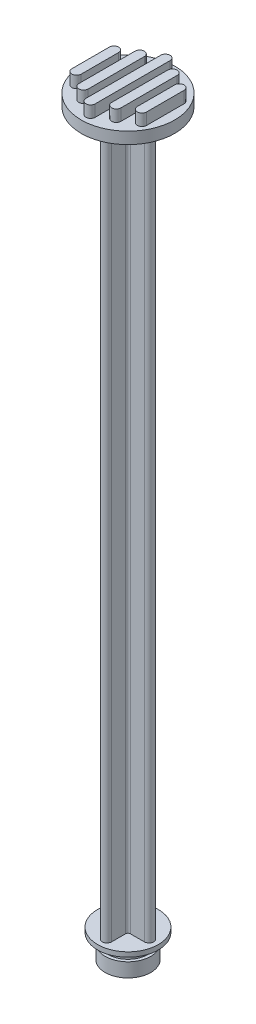
SolidWorks part; units mm, degrees
ref_plane "Front Plane" through (0, 0, 0) normal (0, 0, 1) x (1, 0, 0)
ref_plane "Top Plane" through (0, 0, 0) normal (0, 1, 0) x (1, 0, 0)
ref_plane "Right Plane" through (0, 0, 0) normal (1, 0, 0) x (0, 0, -1)
sketch "Sketch1" plane through (0, 0, 0) normal (0, 0, 1) x (1, 0, 0)
  line L0 (0, 0) -> (4.875, 0)
  line L1 (4.875, 0) -> (4.875, 3)
  line L2 (4.875, 3) -> (4.225, 3)
  line L3 (4.225, 3) -> (4.225, 5)
  line L4 (4.225, 5) -> (6.5, 5)
  line L5 (6.5, 5) -> (6.5, 6)
  line L6 (6.5, 6) -> (0, 6)
  line L7 (0, 6) -> (0, 0)
  dimension "D1" = 6.5
  dimension "D2" = 1
  dimension "D3" = 2
  dimension "D4" = 3
  dimension "D5" = 4.875
  dimension "D6" = 4.225
revolve "Revolve1" add sketch "Sketch1" angle 360 about L7
sketch "Sketch2" plane through (0, 6, 0) normal (0, 1, 0) x (1, 0, 0)
  line L0 (0, 1) -> (0, 0) construction
  line L1 (-1, 0) -> (0, 0) construction
  line L2 (-1, 4.5) -> (-1, 1.5)
  line L3 (-4.5, -1) -> (-1.5, -1)
  line L4 (1, 4.5) -> (1, 1.5)
  line L5 (-4.5, 1) -> (-1.5, 1)
  line L6 (-1, 6.5) -> (-1, -6.5) construction
  line L7 (0, 6.5) -> (0, -6.5) construction
  line L8 (1, 6.5) -> (1, -6.5) construction
  line L9 (-6.5, 1) -> (6.5, 1) construction
  line L10 (-6.5, 0) -> (6.5, 0) construction
  line L11 (-6.5, -1) -> (6.5, -1) construction
  line L12 (1.5, -1) -> (4.5, -1)
  line L13 (0, -1) -> (0, -5.5) construction
  line L14 (1, -1.5) -> (1, -4.5)
  line L15 (1.5, 1) -> (4.5, 1)
  line L16 (-1, -1.5) -> (-1, -4.5)
  arc A1 (1, 4.5) -> (-1, 4.5) centre (0, 4.5) ccw
  arc A2 (4.5, -1) -> (4.5, 1) centre (4.5, 0) ccw
  arc A3 (1, -4.5) -> (-1, -4.5) centre (0, -4.5) cw
  arc A4 (-4.5, -1) -> (-4.5, 1) centre (-4.5, 0) cw
  arc A5 (-1.5, 1) -> (-1, 1.5) centre (-1.5, 1.5) ccw
  arc A6 (1, 1.5) -> (1.5, 1) centre (1.5, 1.5) ccw
  arc A7 (1.5, -1) -> (1, -1.5) centre (1.5, -1.5) ccw
  arc A8 (-1, -1.5) -> (-1.5, -1) centre (-1.5, -1.5) ccw
  point P19 (0, 0)
  point P42 (1, -1)
  point P45 (-1, -1)
  dimension "D5" = 0.5
  dimension "D3" = 4.5
  dimension "D4" = 4.5
  dimension "D1" = 1
  dimension "D2" = 1
extrude "Boss-Extrude1" add sketch "Sketch2" along normal blind 152
sketch "Sketch3" plane through (0, 158, 0) normal (0, 1, 0) x (1, 0, 0)
  circle A0 centre (0, 0) radius 10
  dimension "D1" = 20
extrude "Boss-Extrude2" add sketch "Sketch3" along normal blind 2.5
sketch "Sketch4" plane through (0, 160.5, 0) normal (0, 1, 0) x (1, 0, 0)
  line L0 (0, 6.3392) -> (0, -10) construction
  line L1 (-10, 0) -> (10, 0) construction
  line L2 (-3.5, 4.0448) -> (-3.5, -6.1505) construction
  line L3 (-1, 10) -> (-1, -10) construction
  line L4 (-1, 8) -> (-1, -10)
  line L5 (-4.5, 6) -> (-4.5, -6.1505)
  line L6 (-8, 4) -> (-8, -4)
  line L7 (1, 8) -> (1, -10)
  line L8 (-2.5, 6) -> (-2.5, -6.1505)
  line L9 (-6, -4) -> (-6, 4)
  line L10 (-4.5, 6.5652) -> (-4.5, -6.1505) construction
  line L11 (-3.5, 6.5652) -> (-3.5, -6.1505) construction
  line L12 (-2.5, 6.5652) -> (-2.5, -6.1505) construction
  line L13 (0, 10) -> (0, -10) construction
  line L14 (1, 10) -> (1, -10) construction
  line L15 (7, 0) -> (7, -3.9115) construction
  line L16 (-7, 0) -> (-7, -3.9115) construction
  line L17 (3.5, 4.0448) -> (3.5, -6.1505) construction
  line L18 (6, -4) -> (6, 4)
  line L19 (2.5, 6) -> (2.5, -6.1505)
  line L20 (8, 4) -> (8, -4)
  line L21 (4.5, 6) -> (4.5, -6.1505)
  circle A0 centre (0, 0) radius 10 construction
  arc A1 (1, 8) -> (-1, 8) centre (0, 8) ccw
  arc A2 (-2.5, 6) -> (-4.5, 6) centre (-3.5, 6) ccw
  arc A3 (-6, 4) -> (-8, 4) centre (-7, 4) ccw
  arc A4 (1, -8) -> (-1, -8) centre (0, -8) cw
  arc A5 (-2.5, -6) -> (-4.5, -6) centre (-3.5, -6) cw
  arc A6 (-6, -4) -> (-8, -4) centre (-7, -4) cw
  arc A7 (6, -4) -> (8, -4) centre (7, -4) ccw
  arc A8 (2.5, -6) -> (4.5, -6) centre (3.5, -6) ccw
  arc A9 (6, 4) -> (8, 4) centre (7, 4) cw
  arc A10 (2.5, 6) -> (4.5, 6) centre (3.5, 6) cw
  dimension "D3" = 8
  dimension "D4" = 6
  dimension "D5" = 4
  dimension "D6" = 3.5
  dimension "D7" = 3.5
  dimension "D1" = 1
  dimension "D2" = 1
extrude "Boss-Extrude3" add sketch "Sketch4" along normal blind 2.5 contours A4 L7 A1 L4 | A5 L8 A2 L5 | A10 L19 A8 L21 | A9 L18 A7 L20 | L9 A3 L6 A6
